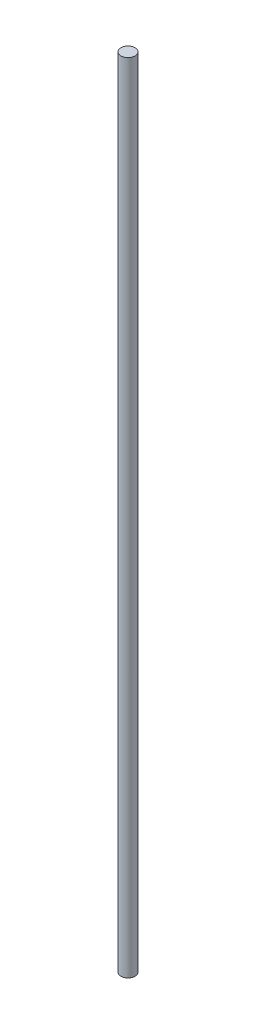
SolidWorks part; units mm, degrees
ref_plane "Alzado" through (0, 0, 0) normal (0, 0, 1) x (1, 0, 0)
ref_plane "Planta" through (0, 0, 0) normal (0, 1, 0) x (1, 0, 0)
ref_plane "Vista lateral" through (0, 0, 0) normal (1, 0, 0) x (0, 0, -1)
sketch "Croquis1" plane through (0, 0, 0) normal (0, 1, 0) x (1, 0, 0)
  circle A0 centre (0, 0) radius 1.524
  dimension "D1" = 3.048
extrude "Saliente-Extruir1" add sketch "Croquis1" along normal blind 177.8
sketch "Croquis2" plane through (0, 0, 0) normal (1, 0, 0) x (0, 0, -1)
  line L0 (-1.524, 177.8) -> (-1.524, 171.0615)
  line L1 (-1.524, 177.8) -> (-1.524, 0) construction
  line L2 (-1.524, 171.0615) -> (1.524, 171.0615)
  line L3 (1.524, 0) -> (1.524, 177.8) construction
  line L4 (1.524, 171.0615) -> (1.524, 177.8)
  line L5 (1.524, 177.8) -> (-1.524, 177.8)
extrude "Cortar-Extruir1" cut sketch "Croquis2" along normal blind 8.128 and the other way blind 7.62
